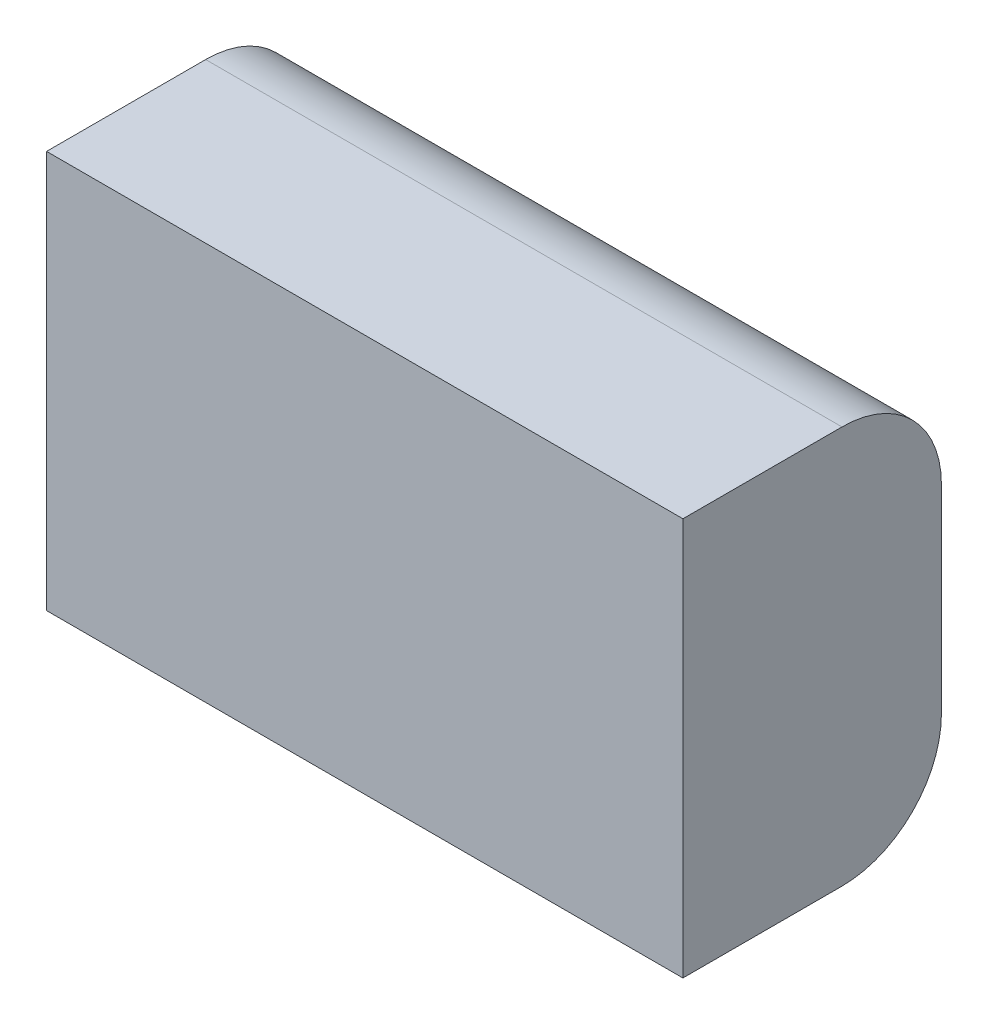
SolidWorks part; units mm, degrees
ref_plane "Front Plane" through (0, 0, 0) normal (0, 0, 1) x (1, 0, 0)
ref_plane "Top Plane" through (0, 0, 0) normal (0, 1, 0) x (1, 0, 0)
ref_plane "Right Plane" through (0, 0, 0) normal (1, 0, 0) x (0, 0, -1)
sketch "Sketch1" plane through (0, 0, 0) normal (1, 0, 0) x (0, 0, -1)
  line L1 (49.3736, 66.0217) -> (-1.4264, 66.0217)
  line L2 (81.1236, 34.2717) -> (81.1236, -29.2283)
  line L3 (49.3736, -60.9783) -> (-1.4264, -60.9783)
  line L4 (-1.4264, 66.0217) -> (-1.4264, -60.9783)
  arc A0 (49.3736, 66.0217) -> (81.1236, 34.2717) centre (49.3736, 34.2717) cw
  arc A1 (81.1236, -29.2283) -> (49.3736, -60.9783) centre (49.3736, -29.2283) cw
  point P8 (81.1236, -60.9783)
  dimension "D3" = 31.75
  dimension "D1" = 127
extrude "Boss-Extrude1" add sketch "Sketch1" along normal mid plane 203.2
equation "\"bumple\"= 24in'bumpler length"
equation "\"D1@Boss-Extrude1\"=(\"robot_width@2016 Chassis 3.0.Assembly\"-\"intake_width@2016 Chassis 3.0.Assembly\")/2"
